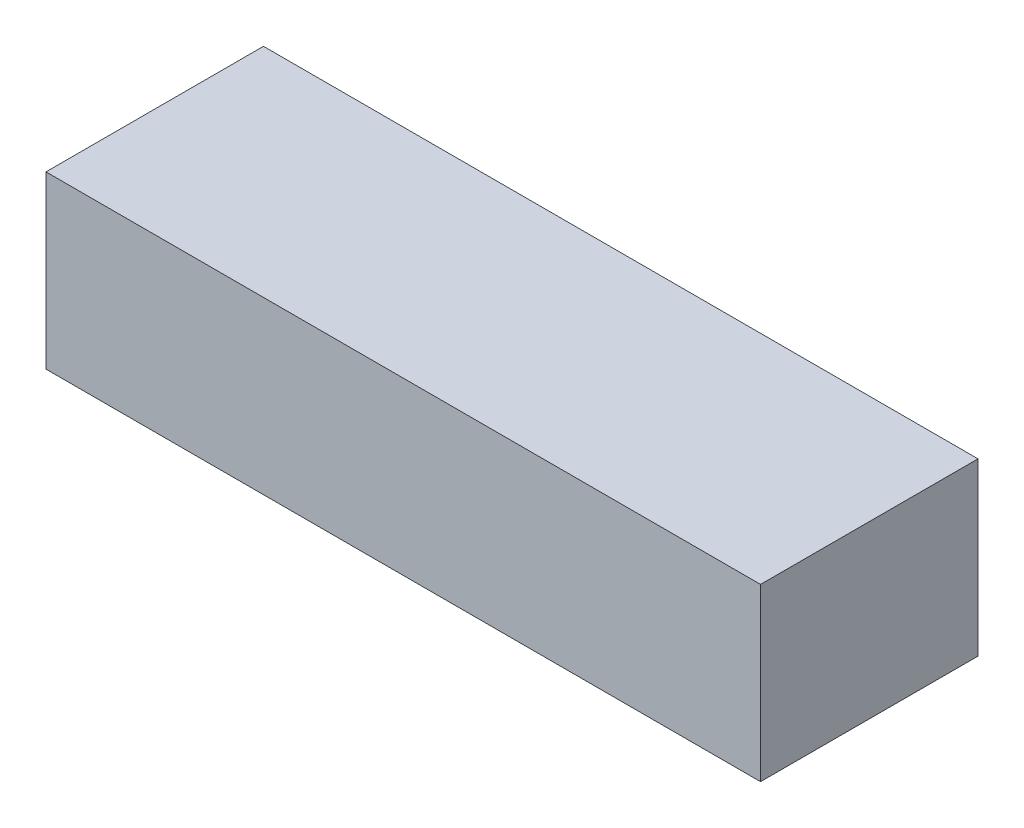
SolidWorks part; units mm, degrees
ref_plane "Front Plane" through (0, 0, 0) normal (0, 0, 1) x (1, 0, 0)
ref_plane "Top Plane" through (0, 0, 0) normal (0, 1, 0) x (1, 0, 0)
ref_plane "Right Plane" through (0, 0, 0) normal (1, 0, 0) x (0, 0, -1)
sketch "Sketch1" plane through (0, 0, 0) normal (1, 0, 0) x (0, 0, -1)
  line L0 (-14, 11) -> (14, -11) construction
  line L1 (-14, 11) -> (14, 11)
  line L2 (-14, 11) -> (-14, -11)
  line L3 (-14, -11) -> (14, -11)
  line L4 (14, 11) -> (14, -11)
  dimension "D1" = 28
  dimension "D2" = 22
extrude "Boss-Extrude1" add sketch "Sketch1" along normal blind 92
